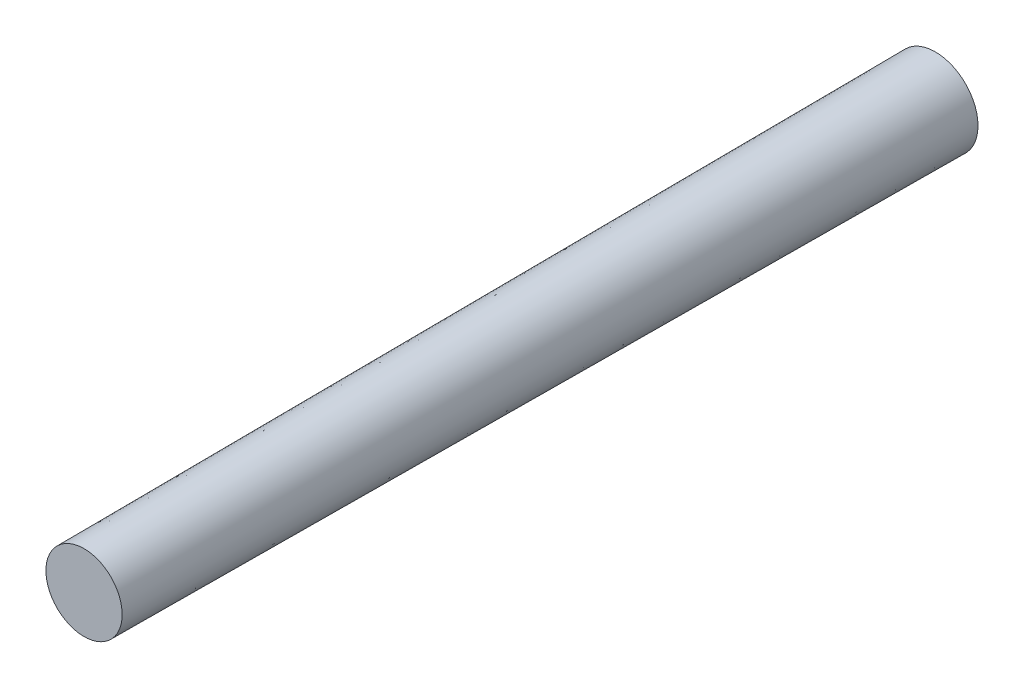
SolidWorks part; units mm, degrees
ref_plane "Front Plane" through (0, 0, 0) normal (0, 0, 1) x (1, 0, 0)
ref_plane "Top Plane" through (0, 0, 0) normal (0, 1, 0) x (1, 0, 0)
ref_plane "Right Plane" through (0, 0, 0) normal (1, 0, 0) x (0, 0, -1)
sketch "Sketch1" plane through (0, 0, 0) normal (0, 0, 1) x (1, 0, 0)
  circle A0 centre (0, 0) radius 3
  dimension "D1" = 6
extrude "Boss-Extrude1" add sketch "Sketch1" along normal blind 60 draft 0.3
